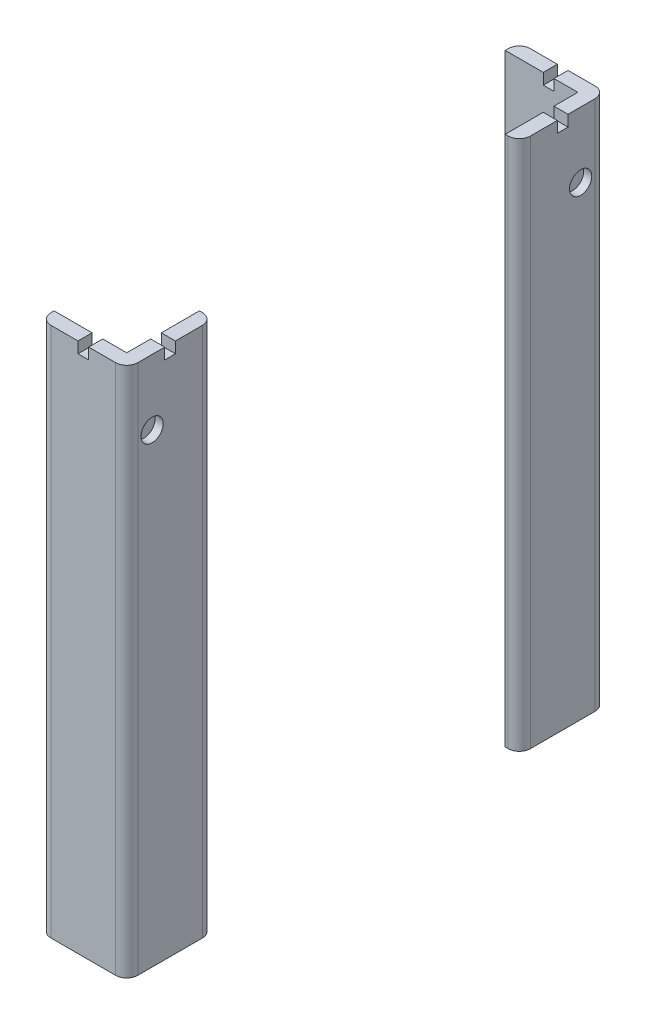
SolidWorks part; units mm, degrees
ref_plane "Front Plane" through (0, 0, 0) normal (0, 0, 1) x (1, 0, 0)
ref_plane "Top Plane" through (0, 0, 0) normal (0, 1, 0) x (1, 0, 0)
ref_plane "Right Plane" through (0, 0, 0) normal (1, 0, 0) x (0, 0, -1)
sketch "Sketch1" plane through (0, 0, 0) normal (0, 0, 1) x (1, 0, 0)
  line L1 (0, 0) -> (-32.7309, 0)
  line L2 (0, 0) -> (0, 237)
  line L3 (0, 237) -> (-32.7309, 237)
  line L4 (-32.7309, 0) -> (-32.7309, 237)
extrude "Boss-Extrude1" add sketch "Sketch1" along normal blind 6.35
sketch "Sketch2" plane through (0, 0, 0) normal (1, 0, 0) x (0, 0, -1)
  line L1 (-6.35, 0) -> (32.73, 0)
  line L2 (-6.35, 0) -> (-6.35, 237)
  line L3 (-6.35, 237) -> (32.73, 237)
  line L4 (32.73, 0) -> (32.73, 237)
  dimension "D1" = 39.08
  dimension "D2" = 237
extrude "Boss-Extrude3" add sketch "Sketch2" along normal blind 6.35
ref_plane "RearMirrorPlane" through (0, 0, -101.6) normal (0, 0, -1) x (-1, 0, 0)
sketch "Sketch27" plane through (6.35, 0, 0) normal (1, 0, 0) x (0, 0, -1)
  line L1 (10.7804, 237) -> (15.5804, 237)
  line L2 (10.7804, 237) -> (10.7804, 232)
  line L3 (10.7804, 232) -> (15.5804, 232)
  line L4 (15.5804, 237) -> (15.5804, 232)
  dimension "D1" = 4.8
  dimension "D2" = 5
extrude "Locking_Mechanism_Cut" cut sketch "Sketch27" against normal up to surface (6.35 mm away) up to face at (0, 118.5, -16.365)
sketch "Sketch29" plane through (6.35, 0, 0) normal (1, 0, 0) x (0, 0, -1)
  line L0 (-6.35, 237) -> (-6.35, 0) construction
  line L1 (-6.35, 110.0869) -> (32.73, 110.0869)
  line L2 (-6.35, 110.0869) -> (-6.35, 109.0869)
  line L3 (-6.35, 109.0869) -> (32.73, 109.0869)
  line L4 (32.73, 110.0869) -> (32.73, 109.0869)
  line L5 (32.73, 0) -> (32.73, 237) construction
  dimension "D1" = 1
extrude "1 mm split" cut sketch "Sketch29" against normal up to surface (39.0809 mm away) up to face at (-32.7309, 118.5, 3.175)
ref_plane "45Degree" through (0, 0, 0) normal (0.7071, 0, -0.7071) x (0, -1, 0)
mirror "LockingMechanismMirror" about plane through (0, 0, 0) normal (0.7071, 0, -0.7071) of "Locking_Mechanism_Cut"
sketch "Sketch32" plane through (6.35, 0, 0) normal (1, 0, 0) x (0, 0, -1)
  circle A0 centre (5.08, 207.536) radius 5
  dimension "D1" = 10
extrude "Locking Mount" add sketch "Sketch32" along normal up to surface (6.35 mm away) separate body
sketch "Sketch33" plane through (12.7, 0, 0) normal (1, 0, 0) x (0, 0, -1)
  circle A0 centre (5.08, 207.536) radius 1.9
  dimension "D1" = 3.8
extrude "M4 Screw Hole" cut sketch "Sketch33" against normal up to surface (6.35 mm away) up to face at (6.35, 204.0217, -13.1852)
mirror "Mirror2" about plane through (0, 0, -101.6) normal (0, 0, -1) of bodies 223 274 246 227 230
sketch "Sketch34" plane through (12.7, 0, 0) normal (1, 0, 0) x (0, 0, -1)
  circle A0 centre (5.08, 207.536) radius 5
extrude "Cut-Extrude1" cut sketch "Sketch34" against normal blind 10
sketch "Sketch36" plane through (12.7, 0, 0) normal (1, 0, 0) x (0, 0, -1)
  circle A0 centre (198.12, 207.536) radius 5
extrude "Cut-Extrude2" cut sketch "Sketch36" against normal blind 10
sketch "Sketch40" plane through (0, 0, -209.55) normal (0, 0, -1) x (-1, 0, 0)
  line L1 (-6.35, 110.0869) -> (32.7309, 110.0869)
  line L2 (-6.35, 110.0869) -> (-6.35, 109.0869)
  line L3 (-6.35, 109.0869) -> (32.7309, 109.0869)
  line L4 (32.7309, 110.0869) -> (32.7309, 109.0869)
extrude "Boss-Extrude4" add sketch "Sketch40" against normal up to surface (6.35 mm away) up to face at (-14.7729, 204.0217, -203.2)
sketch "Sketch41" plane through (6.35, 0, 0) normal (1, 0, 0) x (0, 0, -1)
  line L1 (170.47, 110.0869) -> (203.2, 110.0869)
  line L2 (170.47, 110.0869) -> (170.47, 109.0869)
  line L3 (170.47, 109.0869) -> (203.2, 109.0869)
  line L4 (203.2, 110.0869) -> (203.2, 109.0869)
extrude "Boss-Extrude5" add sketch "Sketch41" against normal up to surface (6.35 mm away) up to face at (0, 204.0217, -188.4273)
sketch "Sketch42" plane through (6.35, 0, 0) normal (1, 0, 0) x (0, 0, -1)
  line L1 (32.73, 110.0869) -> (-6.35, 110.0869)
  line L2 (32.73, 110.0869) -> (32.73, 109.0869)
  line L3 (32.73, 109.0869) -> (-6.35, 109.0869)
  line L4 (-6.35, 110.0869) -> (-6.35, 109.0869)
extrude "Boss-Extrude6" add sketch "Sketch42" against normal up to surface (6.35 mm away) up to face at (0, 204.0217, -14.7727)
sketch "Sketch43" plane through (0, 0, 6.35) normal (0, 0, 1) x (1, 0, 0)
  line L1 (0, 110.0869) -> (-32.7309, 110.0869)
  line L2 (0, 110.0869) -> (0, 109.0869)
  line L3 (0, 109.0869) -> (-32.7309, 109.0869)
  line L4 (-32.7309, 110.0869) -> (-32.7309, 109.0869)
extrude "Boss-Extrude7" add sketch "Sketch43" against normal up to surface (6.35 mm away) up to face at (-14.7729, 204.0217, 0)
sketch "Sketch44" plane through (6.35, 0, 0) normal (1, 0, 0) x (0, 0, -1)
  line L0 (31.9184, -2) -> (31.9184, 47.3364) construction
  line L1 (-6.35, 0) -> (31.9184, 0)
  line L2 (-6.35, 0) -> (-6.35, -2)
  line L3 (-6.35, -2) -> (31.9184, -2)
  line L4 (31.9184, 0) -> (31.9184, -2)
  line L5 (203.2, -2) -> (0, -2) construction
extrude "Boss-Extrude8" add sketch "Sketch44" against normal up to surface (6.35 mm away) up to face at (0, 176.5, -14.7727)
sketch "Sketch45" plane through (0, 0, 6.35) normal (0, 0, 1) x (1, 0, 0)
  line L1 (-32.7309, 0) -> (0, 0)
  line L2 (-32.7309, 0) -> (-32.7309, -2)
  line L3 (-32.7309, -2) -> (0, -2)
  line L4 (0, 0) -> (0, -2)
extrude "Boss-Extrude9" add sketch "Sketch45" against normal up to surface (6.35 mm away) up to face at (-14.7729, 176.5, 0)
fillet "Fillet4" radius 5 3 edges at (6.35, 118.5, -32.73) (-32.7309, 117.5, 6.35) (6.35, 117.5, 6.35)
sketch "Sketch46" plane through (6.35, 0, 0) normal (1, 0, 0) x (0, 0, -1)
  line L1 (170.47, 0) -> (209.55, 0)
  line L2 (170.47, 0) -> (170.47, -2)
  line L3 (170.47, -2) -> (209.55, -2)
  line L4 (209.55, 0) -> (209.55, -2)
extrude "Boss-Extrude10" add sketch "Sketch46" against normal up to surface (6.35 mm away)
sketch "Sketch47" plane through (0, 0, -209.55) normal (0, 0, -1) x (-1, 0, 0)
  line L1 (0, 0) -> (32.7309, 0)
  line L2 (0, 0) -> (0, -2)
  line L3 (0, -2) -> (32.7309, -2)
  line L4 (32.7309, 0) -> (32.7309, -2)
extrude "Boss-Extrude11" add sketch "Sketch47" against normal up to surface (6.35 mm away) up to face at (-14.7729, 176.5, -203.2)
fillet "Fillet5" radius 5 3 edges at (6.35, 117.5, -170.47) (6.35, 117.5, -209.55) (-32.7309, 117.5, -209.55)
